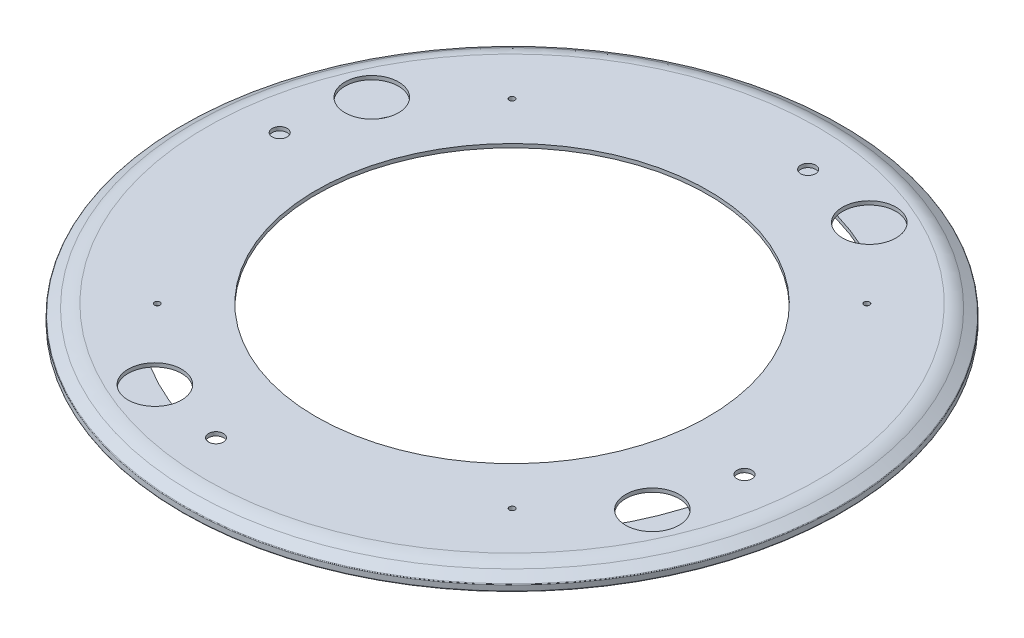
SolidWorks part; units mm, degrees
ref_plane "前视基准面" through (0, 0, 0) normal (0, 0, 1) x (1, 0, 0)
ref_plane "上视基准面" through (0, 0, 0) normal (0, 1, 0) x (1, 0, 0)
ref_plane "右视基准面" through (0, 0, 0) normal (1, 0, 0) x (0, 0, -1)
sketch "草图1" plane through (0, 0, 0) normal (0, 0, 1) x (1, 0, 0)
  line L0 (163.6849, 9) -> (105, 9)
  line L1 (140.5, 0) -> (176, 0)
  line L2 (0, 0) -> (0, -10.6275) construction
  line L3 (176.5, 0.5) -> (176.5, 3.2311)
  line L6 (176.2592, 3.6587) -> (171.0192, 6.8354)
  line L8 (140.5, 0) -> (140.5, 2)
  line L9 (140.5, 2) -> (174.5, 2)
  line L14 (174.5, 2) -> (174.5, 2.6564)
  line L15 (105, 9) -> (105, 7)
  line L16 (168.0963, 6.4391) -> (174.5, 2.6564)
  line L17 (105, 7) -> (163.6849, 7)
  arc A3 (176, 0) -> (176.5, 0.5) centre (176, 0.5) ccw
  arc A4 (163.6849, 9) -> (171.0192, 6.8354) centre (163.6849, -4.5075) cw
  arc A7 (163.6849, 7) -> (168.0963, 6.4391) centre (163.6849, -10.6275) cw
  arc A8 (176.5, 3.2311) -> (176.2592, 3.6587) centre (176, 3.2311) ccw
revolve "旋转1" add sketch "草图1" angle 360 about L2
sketch "草图3" plane through (0, 9, 0) normal (0, 1, 0) x (1, 0, 0)
  circle A1 centre (58.0817, 133.2191) radius 14.3253
  circle A2 centre (133.2191, -58.0817) radius 14.3253
  circle A3 centre (-58.0817, -133.2191) radius 14.3253
  circle A4 centre (-133.2191, 58.0817) radius 14.3253
  point P12 (0, 0)
  dimension "D1" = 4
extrude "切除-拉伸2" cut sketch "草图3" against normal blind 3
sketch "草图4" plane through (0, 9, 0) normal (0, 1, 0) x (1, 0, 0)
  circle A0 centre (17.0535, 141.4979) radius 4
  circle A1 centre (141.4979, -17.0535) radius 4
  circle A2 centre (-17.0535, -141.4979) radius 4
  circle A3 centre (-141.4979, 17.0535) radius 4
  point P11 (0, 0)
  dimension "D1" = 4
extrude "切除-拉伸3" cut sketch "草图4" against normal blind 3
sketch "草图5" plane through (0, 0, 0) normal (0, -1, 0) x (1, 0, 0)
  circle A0 centre (-103.5, 103.5) radius 2.5
  circle A1 centre (103.5, 103.5) radius 2.5
  circle A2 centre (103.5, -103.5) radius 2.5
  circle A3 centre (-103.5, -103.5) radius 2.5
extrude "切除-拉伸4" cut sketch "草图5" against normal blind 2
sketch "草图6" plane through (0, 9, 0) normal (0, 1, 0) x (1, 0, 0)
  circle A0 centre (-95, 95) radius 1.5
  circle A1 centre (95, 95) radius 1.5
  circle A2 centre (95, -95) radius 1.5
  circle A3 centre (-95, -95) radius 1.5
extrude "切除-拉伸5" cut sketch "草图6" against normal blind 3
